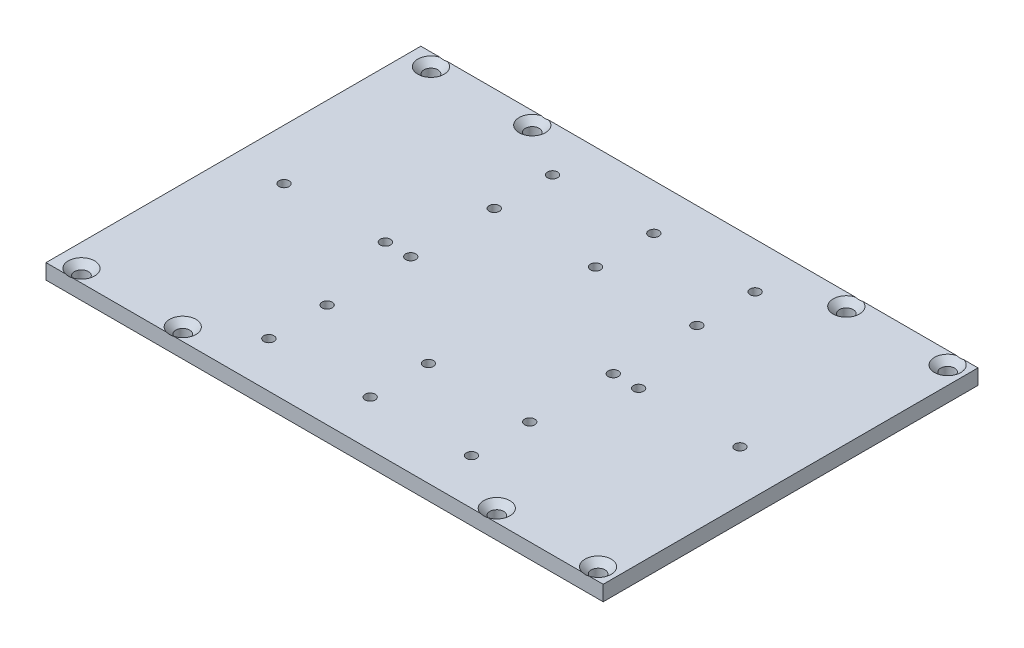
SolidWorks part; units mm, degrees
ref_plane "Front Plane" through (0, 0, 0) normal (0, 0, 1) x (1, 0, 0)
ref_plane "Top Plane" through (0, 0, 0) normal (0, 1, 0) x (1, 0, 0)
ref_plane "Right Plane" through (0, 0, 0) normal (1, 0, 0) x (0, 0, -1)
sketch "Sketch1" plane through (0, 0, 0) normal (0, 1, 0) x (1, 0, 0)
  line L1 (-110, -74) -> (110, -74)
  line L2 (-110, -74) -> (-110, 74)
  line L3 (-110, 74) -> (110, 74)
  line L4 (110, -74) -> (110, 74)
  line L5 (-110, -74) -> (110, 74) construction
  line L6 (-110, 74) -> (110, -74) construction
  point P0 (0, 0)
  dimension "D1" = 148
  dimension "D2" = 220
extrude "Boss-Extrude1" add sketch "Sketch1" along normal blind 6
hole_wizard "CSK for M5 Flat Head Machine Screw2" positions "Sketch5" profile "Sketch4" countersink size "M5" standard "ANSI Metric" end condition through all
sketch "Sketch5" plane through (0, 6, 0) normal (0, 1, 0) x (1, 0, 0)
  line L0 (110, -74) -> (110, 74) construction
  line L1 (-110, -74) -> (110, -74) construction
  point P0 (103, -69)
  point P2 (63, -69)
  point P4 (-101, -69)
  point P6 (-61, -69)
  point P12 (103, 69)
  point P14 (63, 69)
  point P16 (-61, 69)
  point P18 (-101, 69)
  dimension "D1" = 40
  dimension "D2" = 7
  dimension "D3" = 5
  dimension "D4" = 40
  dimension "D5" = 5
  dimension "D6" = 204
  dimension "D7" = 138
  dimension "D8" = 138
  dimension "D9" = 138
  dimension "D10" = 138
  dimension "D11" = 40
  dimension "D12" = 40
sketch "Sketch4" plane through (103, 6, 69) normal (1, 0, 0) x (0, 0, 1)
  line L0 (0, 0) -> (0, 6)
  line L1 (0, 6) -> (2.75, 6)
  line L2 (2.75, 6) -> (2.75, 2.45)
  line L3 (2.75, 2.45) -> (5.2, 0)
  line L5 (5.2, 0) -> (0, 0)
  line L6 (-2.75, 2.45) -> (-5.2, 0) construction
  line L11 (0, -6.35) -> (0, 107.95) construction
  dimension "Thru Hole Dia." = 5.5
  dimension "Thru Hole Depth" = 6
  dimension "Near C'Sink Dia." = 10.4
  dimension "Near C'Sink Angle" = 90
hole_wizard "Ø4.0mm Dowel Hole1" positions "Sketch7" profile "Sketch6" hole size "Ø4.0" standard "ANSI Metric"
sketch "Sketch7" plane through (0, 6, 0) normal (0, 1, 0) x (1, 0, 0)
  line L1 (61.5717, 74) -> (-59.5717, 74) construction
  line L2 (-59.5717, -74) -> (61.5717, -74) construction
  point P0 (0, 56)
  point P2 (0, 33)
  point P4 (0, -33)
  point P6 (0, -56)
  point P23 (-0.7423, 50.3035)
  dimension "D1" = 18
  dimension "D2" = 23
  dimension "D3" = 18
  dimension "D4" = 23
sketch "Sketch6" plane through (0, 6, -56) normal (1, 0, 0) x (0, 0, 1)
  line L0 (0, 0) -> (0, 13.2017)
  line L1 (0, 13.2017) -> (2, 12)
  line L2 (2, 12) -> (2, 0)
  line L5 (2, 0) -> (0, 0)
  line L10 (0, 13.2017) -> (-2, 12) construction
  line L11 (0, -6.35) -> (0, 107.95) construction
  dimension "Hole Dia." = 4
  dimension "Hole Depth" = 12
  dimension "Drill Angle" = 118
hole_wizard "Ø4.0mm Dowel Hole2" positions "Sketch9" profile "Sketch8" hole size "Ø4.0" standard "ANSI Metric"
sketch "Sketch9" plane through (0, 6, 0) normal (0, 1, 0) x (1, 0, 0)
  circle A0 centre (0, 56) radius 2 construction
  circle A1 centre (0, 33) radius 2 construction
  circle A2 centre (0, -33) radius 2 construction
  circle A3 centre (0, -56) radius 2 construction
  point P0 (-40, 33)
  point P2 (-40, 56)
  point P4 (-40, 0)
  point P6 (-50, 0)
  point P8 (-90, 0)
  point P10 (-40, -56)
  point P12 (-40, -33)
  dimension "D1" = 40
  dimension "D2" = 10
  dimension "D3" = 40
  dimension "D4" = 40
  dimension "D5" = 40
  dimension "D6" = 40
  dimension "D7" = 40
sketch "Sketch8" plane through (-40, 6, -33) normal (1, 0, 0) x (0, 0, 1)
  line L0 (0, 0) -> (0, 13.2017)
  line L1 (0, 13.2017) -> (2, 12)
  line L2 (2, 12) -> (2, 0)
  line L5 (2, 0) -> (0, 0)
  line L10 (0, 13.2017) -> (-2, 12) construction
  line L11 (0, -6.35) -> (0, 107.95) construction
  dimension "Hole Dia." = 4
  dimension "Hole Depth" = 12
  dimension "Drill Angle" = 118
mirror "Mirror1" about plane through (0, 0, 0) normal (1, 0, 0) of "Ø4.0mm Dowel Hole2"
